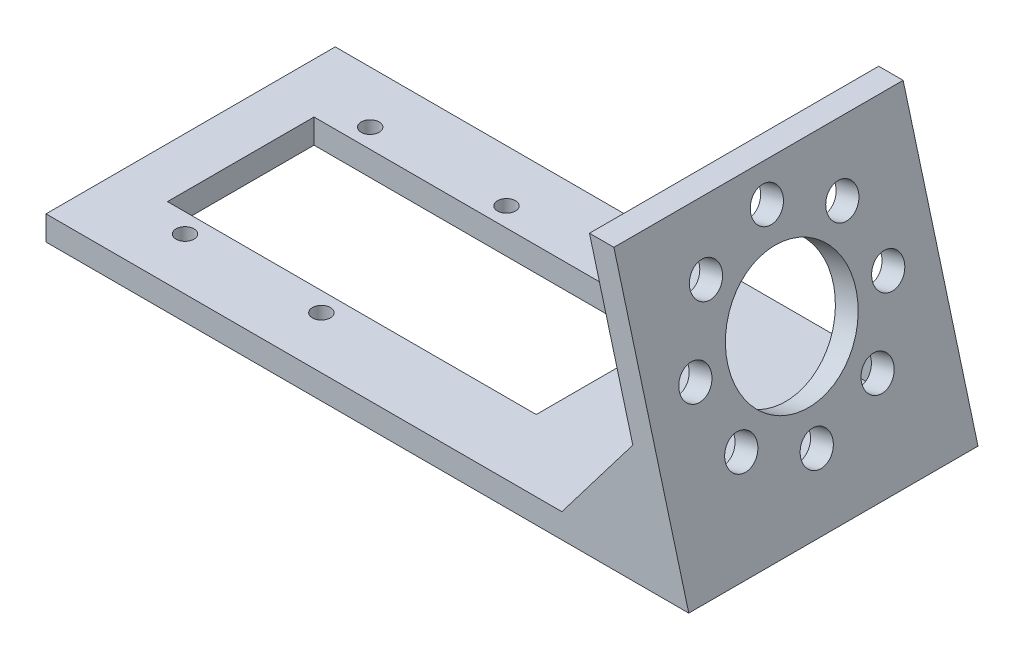
SolidWorks part; units mm, degrees
ref_plane "Front Plane" through (0, 0, 0) normal (0, 0, 1) x (1, 0, 0)
ref_plane "Top Plane" through (0, 0, 0) normal (0, 1, 0) x (1, 0, 0)
ref_plane "Right Plane" through (0, 0, 0) normal (1, 0, 0) x (0, 0, -1)
sketch "Sketch3" plane through (0, 0, 0) normal (0, 0, 1) x (1, 0, 0)
  line L0 (-49.78, 0) -> (77.22, 0)
  line L1 (77.22, 0) -> (62.4285, 55.2027)
  line L2 (62.4285, 55.2027) -> (57.6025, 55.2027)
  line L3 (57.6025, 55.2027) -> (71.1009, 4.826)
  line L4 (71.1009, 4.826) -> (-49.78, 4.826)
  line L5 (-49.78, 4.826) -> (-49.78, 0)
  point P2 (0, 0)
  point P7 (13.72, 0)
  dimension "D1" = 4.826
  dimension "D2" = 4.826
  dimension "D3" = 127
  dimension "D4" = 57.15
  dimension "D5" = 75
extrude "Boss-Extrude1" add sketch "Sketch3" along normal blind 57.15
sketch "Sketch5" plane through (0, 0, 57.15) normal (0, 0, 1) x (1, 0, 0)
  line L0 (71.1009, 4.826) -> (52.1483, 4.826)
  line L1 (71.1009, 4.826) -> (-49.78, 4.826) construction
  line L2 (52.1483, 4.826) -> (66.1704, 23.2269)
  line L3 (57.6025, 55.2027) -> (71.1009, 4.826) construction
  line L10 (-49.78, 4.826) -> (-49.78, 0)
  line L11 (-49.78, 0) -> (77.22, 0)
  line L12 (77.22, 0) -> (62.4285, 55.2027)
  line L13 (62.4285, 55.2027) -> (57.6025, 55.2027)
  line L14 (57.6025, 55.2027) -> (71.1009, 4.826)
  line L15 (71.1009, 4.826) -> (-49.78, 4.826)
  line L16 (-49.78, 4.826) -> (-49.78, 0)
  line L17 (-49.78, 0) -> (77.22, 0)
  line L18 (77.22, 0) -> (62.4285, 55.2027)
  line L19 (62.4285, 55.2027) -> (57.6025, 55.2027)
  line L20 (57.6025, 55.2027) -> (66.1704, 23.2269)
  line L21 (71.1009, 4.826) -> (-49.78, 4.826)
  line M5 (57.6025, 55.2027) -> (71.1009, 4.826)
  line M6 (71.1009, 4.826) -> (-49.78, 4.826)
  dimension "D1" = 19.05
  dimension "D2" = 18.9526
  dimension "D3" = 0
extrude "Boss-Extrude2" add sketch "Sketch5" against normal blind 4.826 contours L2 M6 M5
sketch "Sketch6" plane through (67.5445, 18.0985, 0) normal (-0.9659, -0.2588, 0) x (0, 0, 1)
  line L0 (28.575, 38.4131) -> (28.575, -13.7407) construction
  line L1 (57.15, 38.4131) -> (0, 38.4131) construction
  line L2 (52.324, -13.7407) -> (0, -13.7407) construction
  point P6 (28.575, 12.3362)
ref_plane "Plane1" through (0, 0, 28.575) normal (0, 0, -1) x (0.2588, -0.9659, 0)
mirror "Mirror1" about plane through (0, 0, 28.575) normal (0, 0, -1) of "Boss-Extrude2"
ref_plane "Plane2" through (72.0472, 19.305, 0) normal (0.9659, 0.2588, 0) x (0, 0, -1)
sketch "Sketch9" plane through (72.0472, 19.305, 0) normal (0.9659, 0.2588, 0) x (0, 0, -1)
  line L0 (-28.575, 38.4131) -> (-28.575, -13.7407) construction
  line L1 (-57.15, 37.164) -> (0, 37.164) construction
  circle A0 centre (-28.575, 11.764) radius 12.7
  dimension "D1" = 25.4
  dimension "D2" = 25.4
extrude "Cut-Extrude1" cut sketch "Sketch9" against normal up to next
sketch "Sketch11" plane through (72.0472, 19.305, 0) normal (0.9659, 0.2588, 0) x (0, 0, -1)
  circle A0 centre (-28.575, 30.814) radius 3.175
  dimension "D1" = 6.35
  dimension "D2" = 19.05
extrude "Cut-Extrude2" cut sketch "Sketch11" against normal up to next (4.6616 mm away)
pattern_circular "CirPattern1" count 8 over 360 about axis through (-3.0447, 11.3631, 28.575) along (0.9659, 0.2588, 0) of "Cut-Extrude2"
ref_plane "Plane3" through (0, 4.826, 0) normal (0, 1, 0) x (1, 0, 0)
sketch "Sketch12" plane through (0, 4.826, 0) normal (0, 1, 0) x (1, 0, 0)
  line L0 (-39.874, -6.985) -> (31.246, -6.985) construction
  line L1 (32.9884, -14.097) -> (32.9884, -43.053)
  line L2 (31.246, -50.165) -> (-39.874, -50.165) construction
  line L3 (-39.874, -43.053) -> (-39.874, -14.097)
  line L5 (-49.78, -57.15) -> (-49.78, 0) construction
  line L6 (-39.874, -14.097) -> (32.9884, -14.097)
  line L7 (-39.874, -43.053) -> (32.9884, -43.053)
  line L12 (52.1483, 0) -> (-49.78, 0) construction
  circle A0 centre (-32.5959, -46.863) radius 1.778
  circle A1 centre (-5.6551, -46.863) radius 1.778
  dimension "D8" = 3.556
  dimension "D11" = 26.9408
  dimension "D1" = 43.18
  dimension "D2" = 71.12
  dimension "D3" = 6.985
  dimension "D4" = 9.906
  dimension "D5" = 7.112
  dimension "D6" = 7.112
  dimension "D7" = 72.8624
  dimension "D9" = 7.2781
  dimension "D10" = 3.81
  dimension "D12" = 3.81
extrude "Cut-Extrude4" cut sketch "Sketch12" against normal through all
mirror "Mirror4" about plane through (0, 0, 28.575) normal (0, 0, -1) of "Cut-Extrude4"
ref_plane "Plane4" through (71.5711, 19.1774, 6.0438) normal (0.9627, 0.258, 0.0813) x (0.0841, 0, -0.9965)
